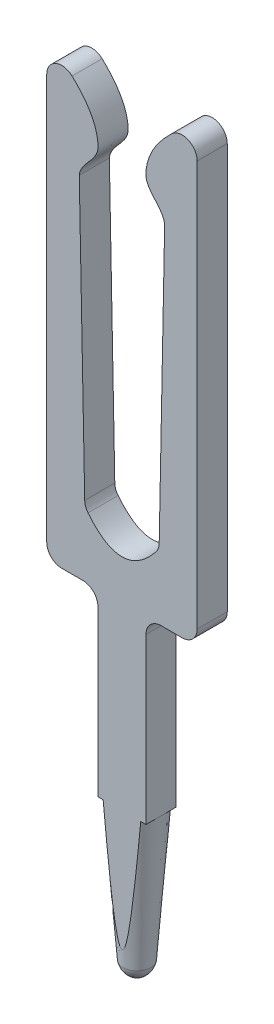
SolidWorks part; units mm, degrees
material "1060 Alloy"
ref_plane "Front Plane" through (0, 0, 0) normal (0, 0, 1) x (1, 0, 0)
ref_plane "Top Plane" through (0, 0, 0) normal (0, 1, 0) x (1, 0, 0)
ref_plane "Right Plane" through (0, 0, 0) normal (1, 0, 0) x (0, 0, -1)
sketch "Sketch1" plane through (0, 0, 0) normal (0, 0, 1) x (1, 0, 0)
  line L0 (-0.32, 1.9994) -> (-0.32, 4.1894)
  line L1 (-0.1839, 0.1844) -> (-0.32, 1.9994)
  line L2 (-0.5677, 9.031) -> (-0.4952, 5.3243)
  line L3 (-1, 4.5894) -> (-1, 9.9798)
  line L4 (0.1839, 0.1844) -> (0.32, 1.9994)
  line L5 (0.32, 1.9994) -> (0.32, 4.1894)
  line L6 (0.52, 4.3894) -> (0.8, 4.3894)
  line L7 (1, 4.5894) -> (1, 9.9798)
  line L8 (0.5677, 9.031) -> (0.4952, 5.3243)
  line L9 (-0.52, 4.3894) -> (-0.8, 4.3894)
  line L10 (0, 4.9226) -> (0, 0) construction
  arc A0 (0, 0) -> (-0.1839, 0.1844) centre (0.0156, 0.1994) cw
  arc A1 (-0.4952, 5.3243) -> (-0.4511, 5.2028) centre (-0.2953, 5.3282) ccw
  arc A2 (-1, 9.9798) -> (-0.663, 10.1256) centre (-0.8, 9.9798) cw
  arc A3 (-0.8, 4.3894) -> (-1, 4.5894) centre (-0.8, 4.5894) cw
  arc A4 (0, 0) -> (0.1839, 0.1844) centre (-0.0156, 0.1994) ccw
  arc A5 (0.32, 4.1894) -> (0.52, 4.3894) centre (0.52, 4.1894) cw
  arc A6 (0.8, 4.3894) -> (1, 4.5894) centre (0.8, 4.5894) ccw
  arc A7 (1, 9.9798) -> (0.663, 10.1256) centre (0.8, 9.9798) ccw
  arc A8 (0.4952, 5.3243) -> (0.4511, 5.2028) centre (0.2953, 5.3282) cw
  arc A9 (-0.32, 4.1894) -> (-0.52, 4.3894) centre (-0.52, 4.1894) ccw
  spline S0 degree 3 poles (0.663, 10.1256) (0.4876, 9.9607) (0.3262, 9.7388) (0.3107, 9.3109) (0.5485, 9.1986) (0.5677, 9.031) knots 0.253308 0.253308 0.253308 0.253308 0.663172 0.707067 1 1 1 1
  spline S1 degree 2 poles (-0.4511, 5.2028) (0, 4.6424) (0.4511, 5.2028) knots 0.043405 0.043405 0.043405 0.956595 0.956595 0.956595
  spline S2 degree 3 poles (-0.663, 10.1256) (-0.4876, 9.9607) (-0.3262, 9.7388) (-0.3107, 9.3109) (-0.5485, 9.1986) (-0.5677, 9.031) knots 0.253308 0.253308 0.253308 0.253308 0.663172 0.707067 1 1 1 1
  dimension "D2" = 0.2
  dimension "D7" = 0.2
  dimension "D8" = 0.68
  dimension "D10" = 0.2
  dimension "D13" = 0.2
  dimension "D3" = 0.1839
  dimension "D4" = 1.815
  dimension "D5" = 0.5332
  dimension "D6" = 2.19
  dimension "D9" = 5.3904
  dimension "D11" = 0.8134
  dimension "D12" = 0.1215
  dimension "D14" = 0.4323
  dimension "D15" = 0.337
  dimension "D16" = 0.9489
  dimension "D17" = 0.5048
extrude "Boss-Extrude1" add sketch "Sketch1" against normal mid plane 0.4
ref_axis "Axis1" through (0, 4.9226, 0) along (0, -1, 0)
sketch "Esquisse1" plane through (0, 0, 0) normal (0, 0, 1) x (1, 0, 0)
  line L2 (1, -0.5006) -> (0, -0.5006)
  line L3 (0, -0.5006) -> (0, 0)
  line L6 (0, 4.9226) -> (0, 0) construction
  line L8 (0.1839, 0.1844) -> (0.32, 1.9994)
  line L9 (0.32, 1.9994) -> (1, 1.9994)
  line L11 (1, 1.9994) -> (1, -0.5006)
  arc A0 (0, 0) -> (0.1839, 0.1844) centre (-0.0347, 0.2185) ccw
  dimension "D3" = 0.2212
  dimension "D1" = 2.5
  dimension "D2" = 1
revolve "Enlèvement de matière-Révolution1" cut sketch "Esquisse1" angle 360 about axis through (0, 4.9226, 0) along (0, -1, 0)
